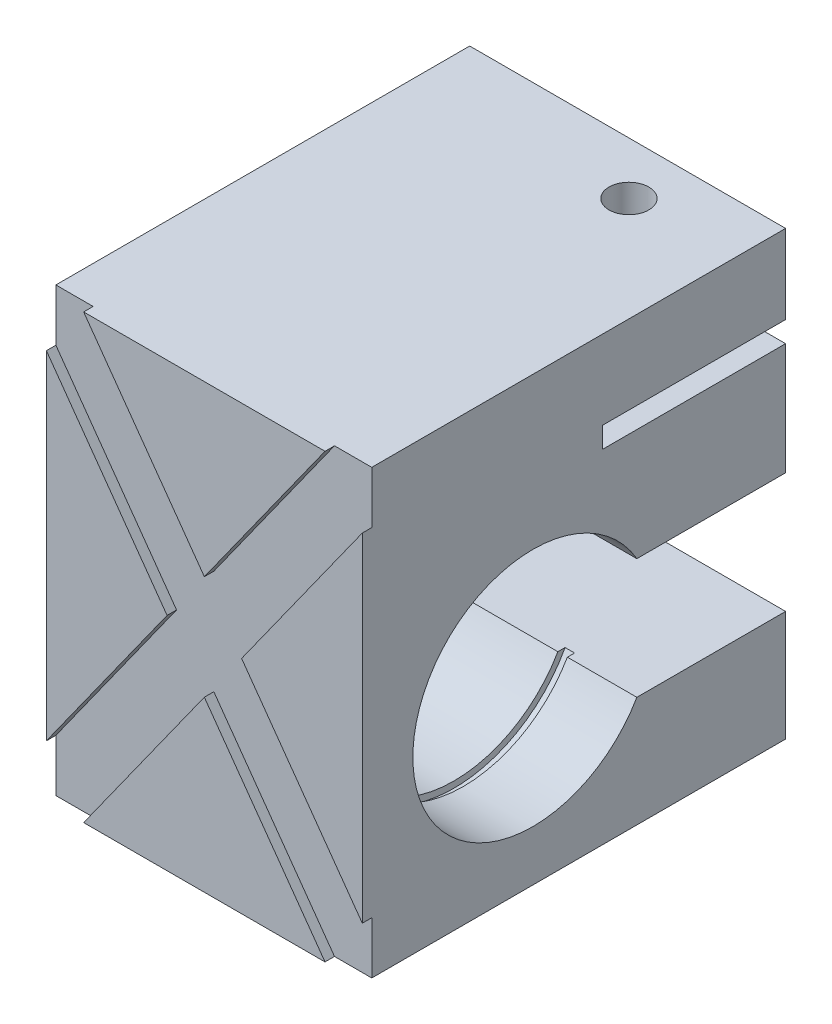
SolidWorks part; units mm, degrees
material "AISI 1020"
ref_plane "Front Plane" through (0, 0, 0) normal (0, 0, 1) x (1, 0, 0)
ref_plane "Top Plane" through (0, 0, 0) normal (0, 1, 0) x (1, 0, 0)
ref_plane "Right Plane" through (0, 0, 0) normal (1, 0, 0) x (0, 0, -1)
sketch "Sketch1" plane through (0, 0, 0) normal (0, 0, 1) x (1, 0, 0)
  line L1 (0, 0) -> (50, 0)
  line L2 (0, 0) -> (0, 70)
  line L3 (0, 70) -> (50, 70)
  line L4 (50, 0) -> (50, 70)
  dimension "D1" = 50
  dimension "D2" = 70
extrude "Boss-Extrude1" add sketch "Sketch1" along normal mid plane 67
sketch "Sketch2" plane through (0, 0, 33.5) normal (0, 0, 1) x (1, 0, 0)
  line L0 (53.9059, 2.7899) -> (3.9059, 72.7899)
  line L1 (53.9059, 2.7899) -> (46.0941, -2.7899)
  line L2 (3.9059, 72.7899) -> (-3.9059, 67.2101)
  line L3 (46.0941, -2.7899) -> (-3.9059, 67.2101)
  line L4 (53.9059, 2.7899) -> (-3.9059, 67.2101) construction
  line L5 (3.9059, 72.7899) -> (46.0941, -2.7899) construction
  line L6 (-3.9059, 2.7899) -> (46.0941, 72.7899)
  line L7 (-3.9059, 2.7899) -> (3.9059, -2.7899)
  line L8 (46.0941, 72.7899) -> (53.9059, 67.2101)
  line L9 (3.9059, -2.7899) -> (53.9059, 67.2101)
  line L10 (-3.9059, 2.7899) -> (53.9059, 67.2101) construction
  line L11 (46.0941, 72.7899) -> (3.9059, -2.7899) construction
  line L12 (25, 70) -> (25, 0) construction
  line L13 (50, 70) -> (0, 70) construction
  line L14 (0, 0) -> (50, 0) construction
  line L15 (0, 35) -> (50, 35) construction
  line L16 (0, 70) -> (0, 0) construction
  line L17 (50, 0) -> (50, 70) construction
  point P1 (25, 35)
  point P2 (25, 35)
  point P22 (0, 0)
  point P23 (0, 0)
  point P28 (56.0968, 64.9377)
  point P29 (50, 70)
  point P30 (0, 70)
  line M7 (0, 70) -> (0, 0)
  line M8 (0, 0) -> (50, 0)
  line M9 (50, 0) -> (50, 70)
  line M10 (50, 70) -> (0, 70)
  dimension "D1" = 9.6
extrude "Cut-Extrude2" cut sketch "Sketch2" against normal blind 1.5 contours L3 L6 L0 M10 M7 | L9 L3 L0 M8 M9 | L0 L9 L6 M9 M10 | L9 L3 L6 M8 M7 | L3 L9 L0 L6
sketch "Sketch3" plane through (50, 0, 0) normal (1, 0, 0) x (0, 0, -1)
  line L0 (33.5, 0) -> (33.5, 70) construction
  line L1 (4.5, 57.5) -> (33.5, 57.5)
  line L2 (4.5, 57.5) -> (4.5, 54.2)
  line L3 (4.5, 54.2) -> (33.5, 54.2)
  line L4 (33.5, 57.5) -> (33.5, 54.2)
  line L5 (-32, 70) -> (33.5, 70) construction
  dimension "D1" = 29
  dimension "D2" = 3.3
  dimension "D3" = 12.5
extrude "Cut-Extrude3" cut sketch "Sketch3" against normal through all
sketch "Sketch4" plane through (50, 0, 0) normal (1, 0, 0) x (0, 0, -1)
  line L0 (33.5, 36.5) -> (9.9545, 36.5)
  line L1 (33.5, 0) -> (33.5, 54.2) construction
  line L2 (9.9545, 17.5) -> (33.5, 17.5)
  line L3 (-33.5, 8.2582) -> (-33.5, 61.7418) construction
  line L4 (-32, 0) -> (33.5, 0) construction
  line L5 (33.5, 36.5) -> (33.5, 17.5)
  line L6 (-6.5, 27) -> (33.5, 27) construction
  arc A0 (9.9545, 36.5) -> (9.9545, 17.5) centre (-6.5, 27) ccw
  dimension "D2" = 27
  dimension "D3" = 38
  dimension "D4" = 27
  dimension "D1" = 19
extrude "Cut-Extrude4" cut sketch "Sketch4" against normal through all
sketch "Sketch12" plane through (0, 70, 0) normal (0, 1, 0) x (1, 0, 0)
  line L0 (0, -32) -> (0, 33.5) construction
  line L1 (50, 33.5) -> (0, 33.5) construction
  point P0 (33.5, 25.2)
  dimension "D1" = 33.5
  dimension "D2" = 8.3
hole_wizard "Ø6.0mm Dowel Hole2" positions "Sketch12" profile "Sketch11" hole size "Ø6.0" standard "ISO" end condition up to next
sketch "Sketch11" plane through (33.5, 70, -25.2) normal (1, 0, 0) x (0, 0, 1)
  line L0 (0, 0) -> (0, 12.5)
  line L1 (0, 12.5) -> (3.15, 12.5)
  line L2 (3.15, 12.5) -> (3.15, 0)
  line L5 (3.15, 0) -> (0, 0)
  line L11 (0, -6.35) -> (0, 107.95) construction
  dimension "Thru Hole Dia." = 6.3
  dimension "Thru Hole Depth" = 12.5
ref_plane "Plane2" through (37.5, 0, 0) normal (1, 0, 0) x (0, 0, -1)
sketch "Sketch15" plane through (37.5, 0, 0) normal (1, 0, 0) x (0, 0, -1)
  line L0 (9.9545, 36.5) -> (11.0997, 36.5)
  line L1 (9.9545, 17.5) -> (11.0997, 17.5)
  arc A0 (9.9545, 36.5) -> (9.9545, 17.5) centre (-6.5, 27) ccw construction
  arc A1 (9.9545, 36.5) -> (9.9545, 17.5) centre (-6.5, 27) ccw
  arc A2 (11.0997, 36.5) -> (11.0997, 17.5) centre (-6.5, 27) ccw
  dimension "D1" = 40
extrude "Cut-Extrude6" cut sketch "Sketch15" along normal blind 1.5
ref_plane "Plane3" through (25, 0, 0) normal (1, 0, 0) x (0, 0, -1)
mirror "Mirror2" about plane through (25, 0, 0) normal (1, 0, 0) of "Cut-Extrude6"
equation "\"A\"= 50"
equation "\"B\"= 70"
equation "\"D1@Sketch1\"=\"A\""
equation "\"D2@Sketch1\"=\"B\""
